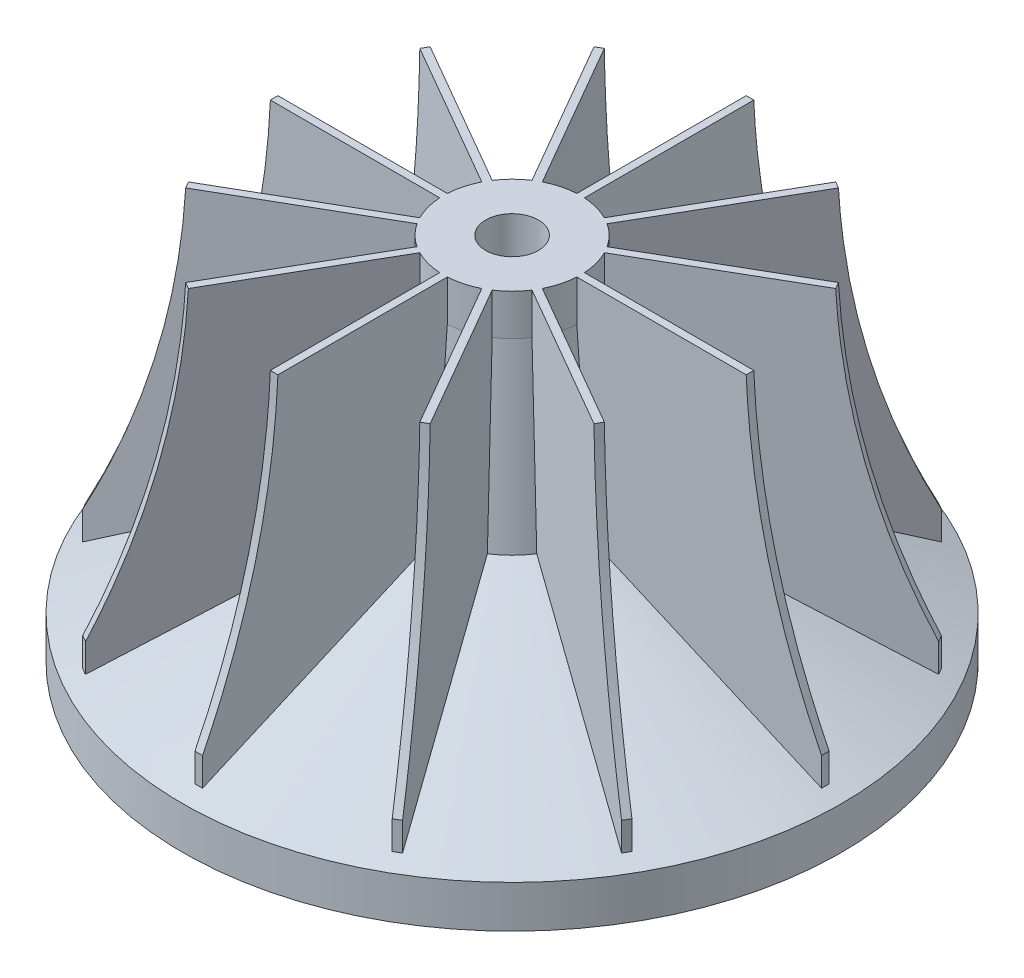
SolidWorks part; units mm, degrees
ref_plane "Front Plane" through (0, 0, 0) normal (0, 0, 1) x (1, 0, 0)
ref_plane "Top Plane" through (0, 0, 0) normal (0, 1, 0) x (1, 0, 0)
ref_plane "Right Plane" through (0, 0, 0) normal (1, 0, 0) x (0, 0, -1)
sketch "Sketch1" plane through (0, 0, 0) normal (0, 0, 1) x (1, 0, 0)
  line L7 (0, 0) -> (0, 37.1175) construction
  line L8 (0, 0) -> (-39.624, 0)
  line L9 (-39.624, 0) -> (-39.624, 5.08)
  line L11 (-39.624, 5.08) -> (-9.8229, 18.0693)
  line L12 (-9.8229, 18.0693) -> (-8.255, 39.5182)
  line L13 (-8.255, 39.5182) -> (-8.255, 44.45)
  line L14 (-8.255, 44.45) -> (0, 44.45)
  line L15 (0, 44.45) -> (0, 0)
  point P1 (-10.7068, 21.4281)
  point P10 (0, 0)
  point P11 (0, 0)
  point P12 (-34.3856, 5.08)
  point P13 (0, 0)
  point P14 (0, 0)
  point P15 (-34.4399, 5.08)
  point P16 (0, 0)
  point P17 (0, 0)
  point P18 (-34.4399, 5.08)
  point P19 (0, 0)
  point P20 (-34.4399, 5.08)
  point P21 (-34.4399, 5.08)
  point P22 (-39.624, 5.4462)
  point P23 (-9.8229, 18.0693)
  dimension "D1" = 39.624
  dimension "D2" = 8.255
  dimension "D3" = 44.45
  dimension "D4" = 5.08
revolve "Revolve1" add sketch "Sketch1" angle 360 about L7
ref_plane "Plane1" through (0, 44.45, 0) normal (0, 1, 0) x (1, 0, 0)
sketch "Sketch3" plane through (0, 44.45, 0) normal (0, 1, 0) x (1, 0, 0)
  line L6 (0.4559, -37.6702) -> (0.456, -8.2062)
  line L7 (-0.4559, -37.6702) -> (-0.4559, -8.2062)
  line L9 (-0.4559, -37.6702) -> (0.4559, -37.6702)
  line L12 (0, -55) -> (0, 55) construction
  circle A2 centre (0, 0) radius 8.255 construction
  spline S0 degree 2 poles (-0.4559, -8.2062) (0, -8.3038) (0.456, -8.2062) knots 0 0 0 1 1 1
  dimension "D1" = 29.464
extrude "Boss-Extrude5" add sketch "Sketch3" against normal up to next
pattern_circular "CirPattern8" count 12 over 360 about axis through (0, 0, 0) along (0, 1, 0) of "Boss-Extrude5"
sketch "Sketch7" plane through (0, 0, 0) normal (1, 0, 0) x (0, 0, -1)
  line L1 (-37.6702, 5.9304) -> (-37.6702, 44.45) construction
  line L2 (-42.1334, 53.4862) -> (-28.575, 53.4862)
  line L4 (0, 0) -> (0, 61.1174) construction
  line L6 (-42.1334, 53.4862) -> (-42.6847, 9.3395)
  line L7 (-42.6847, 9.3395) -> (-37.6702, 9.3395)
  line L8 (-28.575, 53.4862) -> (-28.575, 45.2583)
  spline S0 degree 2 poles (-28.575, 45.2583) (-29.26, 26.3077) (-37.6702, 9.3395) knots 0 0 0 1 1 1
  point P11 (-28.575, 45.2583)
  dimension "D1" = 28.575
revolve "Cut-Revolve3" cut sketch "Sketch7" angle 360 about L4
sketch "Sketch4" plane through (0, 0, 0) normal (1, 0, 0) x (0, 0, -1)
  line L5 (0, 0) -> (0, 72.6591) construction
  line L6 (-18.4402, 47.752) -> (-8.255, 47.752)
  line L8 (-8.255, 47.752) -> (-8.255, 53.2514)
  line L10 (-18.4402, 5.9304) -> (-18.4402, 9.3395) construction
  line L13 (-37.6702, 5.9304) -> (-37.6702, 9.3395) construction
  line L14 (-37.6702, 7.8709) -> (-37.6702, 53.2514)
  line L17 (-37.6702, 53.2514) -> (-8.255, 53.2514)
  arc A0 (-37.6702, 7.8709) -> (-18.4402, 47.752) centre (-68.3352, 47.2337) ccw
  dimension "D2" = 8.255
sketch "Sketch6" plane through (0, 44.45, 0) normal (0, 1, 0) x (1, 0, 0)
  circle A0 centre (0, 0) radius 3.175
  dimension "D1" = 6.35
extrude "Cut-Extrude1" cut sketch "Sketch6" against normal up to next
equation "\"1.90n\"=2"
